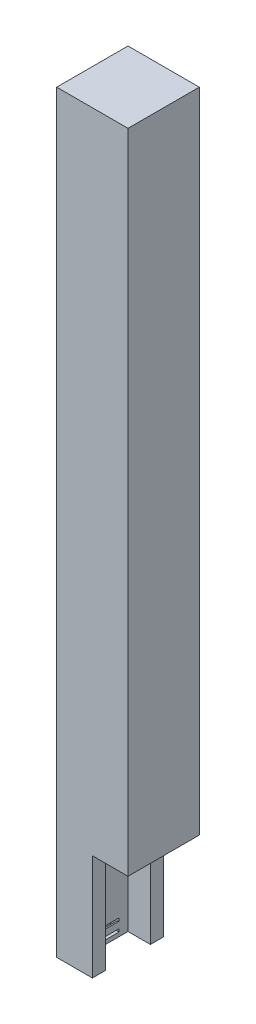
SolidWorks part; units mm, degrees
ref_plane "Front Plane" through (0, 0, 0) normal (0, 0, 1) x (1, 0, 0)
ref_plane "Top Plane" through (0, 0, 0) normal (0, 1, 0) x (1, 0, 0)
ref_plane "Right Plane" through (0, 0, 0) normal (1, 0, 0) x (0, 0, -1)
sketch "Sketch1" plane through (0, 0, 0) normal (0, 1, 0) x (1, 0, 0)
  line L1 (-6.35, -6.35) -> (6.35, -6.35)
  line L2 (-6.35, -6.35) -> (-6.35, 6.35)
  line L3 (-6.35, 6.35) -> (6.35, 6.35)
  line L4 (6.35, -6.35) -> (6.35, 6.35)
  line L5 (-6.35, -6.35) -> (6.35, 6.35) construction
  line L6 (-6.35, 6.35) -> (6.35, -6.35) construction
  point P0 (0, 0)
  dimension "D1" = 12.7
  dimension "D2" = 12.7
sketch "Sketch2" plane through (0, 0, 0) normal (0, 1, 0) x (1, 0, 0)
  line L1 (-11.1125, -11.1125) -> (11.1125, -11.1125)
  line L2 (-11.1125, -11.1125) -> (-11.1125, 11.1125)
  line L3 (-11.1125, 11.1125) -> (11.1125, 11.1125)
  line L4 (11.1125, -11.1125) -> (11.1125, 11.1125)
  line L5 (-11.1125, -11.1125) -> (11.1125, 11.1125) construction
  line L6 (-11.1125, 11.1125) -> (11.1125, -11.1125) construction
  line L11 (-6.35, -6.35) -> (6.35, 6.35) construction
  line L12 (-6.35, 6.35) -> (6.35, -6.35) construction
  line L13 (-6.985, -6.985) -> (6.985, -6.985)
  line L14 (-6.985, -6.985) -> (-6.985, 6.985)
  line L15 (-6.985, 6.985) -> (6.985, 6.985)
  line L16 (6.985, -6.985) -> (6.985, 6.985)
  line L17 (-6.985, -6.985) -> (6.985, 6.985) construction
  line L18 (-6.985, 6.985) -> (6.985, -6.985) construction
  point P0 (0, 0)
  point P6 (0, 0)
  point P12 (0, 0)
  dimension "D1" = 22.225
  dimension "D2" = 13.97
extrude "Boss-Extrude1" add sketch "Sketch2" along normal blind 6.35
sketch "Sketch3" plane through (-6.985, 0, 0) normal (1, 0, 0) x (0, 0, -1)
  line L0 (6.985, 6.35) -> (-6.985, 0) construction
  line L1 (6.985, 6.35) -> (-6.985, 6.35) construction
  line L2 (6.985, 6.35) -> (6.985, 0) construction
  line L3 (6.985, 0) -> (-6.985, 0) construction
  line L4 (-6.985, 6.35) -> (-6.985, 0) construction
  line L5 (-6.985, 6.35) -> (6.985, 0) construction
  line L7 (-4.191, 5.08) -> (4.191, 5.08)
  line L8 (-4.191, 5.08) -> (-4.191, 1.27)
  line L9 (-4.191, 1.27) -> (4.191, 1.27)
  line L10 (4.191, 5.08) -> (4.191, 1.27)
  line L11 (-4.191, 5.08) -> (4.191, 1.27) construction
  line L12 (-4.191, 1.27) -> (4.191, 5.08) construction
  point P6 (0, 3.175)
  dimension "D1" = 3.81
extrude "Cut-Extrude1" cut sketch "Sketch3" against normal blind 2.54
sketch "Sketch4" plane through (0, 0, 4.191) normal (0, 0, -1) x (-1, 0, 0)
  line L0 (6.985, 5.08) -> (6.985, 1.27) construction
  line L1 (6.985, 4.191) -> (6.985, 2.159)
  arc A0 (6.985, 2.159) -> (6.985, 4.191) centre (6.985, 3.175) ccw
  dimension "D1" = 2.032
extrude "Boss-Extrude2" add sketch "Sketch4" along normal up to surface (8.382 mm away) up to face at (-8.255, 3.175, -4.191)
sketch "Sketch6" plane through (0, 6.35, 0) normal (0, 1, 0) x (1, 0, 0)
  line L0 (6.985, 6.985) -> (-6.985, 6.985) construction
  line L1 (-11.1125, -11.1125) -> (11.1125, -11.1125)
  line L2 (-11.1125, -11.1125) -> (-11.1125, 11.1125)
  line L3 (-11.1125, 11.1125) -> (11.1125, 11.1125)
  line L4 (11.1125, -11.1125) -> (11.1125, 11.1125)
  line L5 (-11.1125, -11.1125) -> (11.1125, 11.1125) construction
  line L6 (-11.1125, 11.1125) -> (11.1125, -11.1125) construction
  line L7 (-6.985, -6.985) -> (6.985, -6.985)
  line L8 (-6.985, -6.985) -> (-6.985, 6.985)
  line L9 (-6.985, 6.985) -> (6.985, 6.985)
  line L10 (6.985, -6.985) -> (6.985, 6.985)
  line L11 (-6.985, -6.985) -> (6.985, 6.985) construction
  line L12 (-6.985, 6.985) -> (6.985, -6.985) construction
  line L13 (6.985, -6.985) -> (6.985, 6.985) construction
  point P0 (0, 0)
  point P7 (0, 0)
extrude "Boss-Extrude3" add sketch "Sketch6" along direction (0, -1, 0) on the side of the normal blind 222.25
sketch "Sketch7" plane through (0, 228.6, 0) normal (0, 1, 0) x (1, 0, 0)
  line L1 (-11.1125, -11.1125) -> (11.1125, -11.1125)
  line L2 (-11.1125, -11.1125) -> (-11.1125, 11.1125)
  line L3 (-11.1125, 11.1125) -> (11.1125, 11.1125)
  line L4 (11.1125, -11.1125) -> (11.1125, 11.1125)
  line L5 (-11.1125, -11.1125) -> (11.1125, 11.1125) construction
  line L6 (-11.1125, 11.1125) -> (11.1125, -11.1125) construction
  point P0 (0, 0)
extrude "Boss-Extrude4" add sketch "Sketch7" along normal blind 6.35
sketch "Sketch8" plane through (0, 0, 0) normal (0, -1, 0) x (1, 0, 0)
  line L0 (11.1125, -11.1125) -> (-11.1125, -11.1125) construction
  line L1 (11.1125, 11.1125) -> (0, 11.1125)
  line L2 (11.1125, 11.1125) -> (11.1125, -11.1125)
  line L3 (11.1125, -11.1125) -> (0, -11.1125)
  line L4 (0, 11.1125) -> (0, -11.1125)
extrude "Cut-Extrude2" cut sketch "Sketch8" against normal blind 33.02
